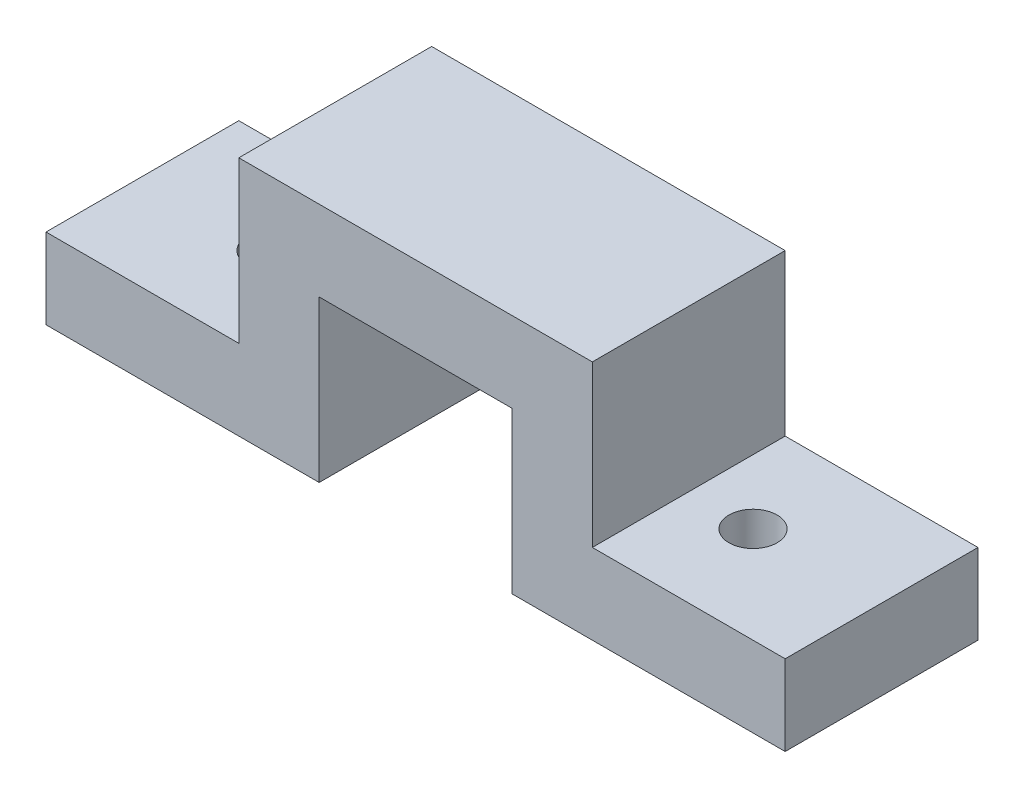
SolidWorks part; units mm, degrees
ref_plane "前视" through (0, 0, 0) normal (0, 0, 1) x (1, 0, 0)
ref_plane "上视" through (0, 0, 0) normal (0, 1, 0) x (1, 0, 0)
ref_plane "右视" through (0, 0, 0) normal (1, 0, 0) x (0, 0, -1)
sketch "草图1" plane through (0, 0, 0) normal (0, 0, 1) x (1, 0, 0)
  line L0 (0, 81.1666) -> (0, -66.8711) construction
  line L1 (15, 38.5978) -> (15, -32.2443) construction
  line L2 (-11, 15) -> (11, 15)
  line L3 (11, 15) -> (11, 5)
  line L4 (11, 5) -> (23, 5)
  line L5 (23, 5) -> (23, 0)
  line L6 (23, 0) -> (6, 0)
  line L7 (6, 0) -> (6, 10)
  line L8 (6, 10) -> (-6, 10)
  line L9 (-15, 38.5978) -> (-15, -32.2443) construction
  line L10 (-6, 0) -> (-6, 10)
  line L11 (-23, 0) -> (-6, 0)
  line L12 (-23, 5) -> (-23, 0)
  line L13 (-11, 5) -> (-23, 5)
  line L14 (-11, 15) -> (-11, 5)
  point P16 (0, 10)
  point P21 (0, 15)
  dimension "D1" = 5
  dimension "D2" = 5
  dimension "D3" = 5
  dimension "D4" = 15
  dimension "D5" = 10
  dimension "D6" = 12
  dimension "D7" = 6
extrude "凸台-拉伸1" add sketch "草图1" along normal blind 12
sketch "草图2" plane through (0, 0, 0) normal (0, 1, 0) x (1, 0, 0)
  line L0 (23, -12) -> (11, -12) construction
  line L2 (-15, 1.8076) -> (-15, -7.5) construction
  circle A0 centre (-15, -6) radius 1.5
  circle A1 centre (15, -6) radius 1.5
  dimension "D1" = 3
  dimension "D2" = 15
  dimension "D3" = 15
  dimension "D4" = 3
  dimension "D5" = 6
extrude "Cut-Extrude3" cut sketch "草图2" against normal blind 10 and the other way through all
